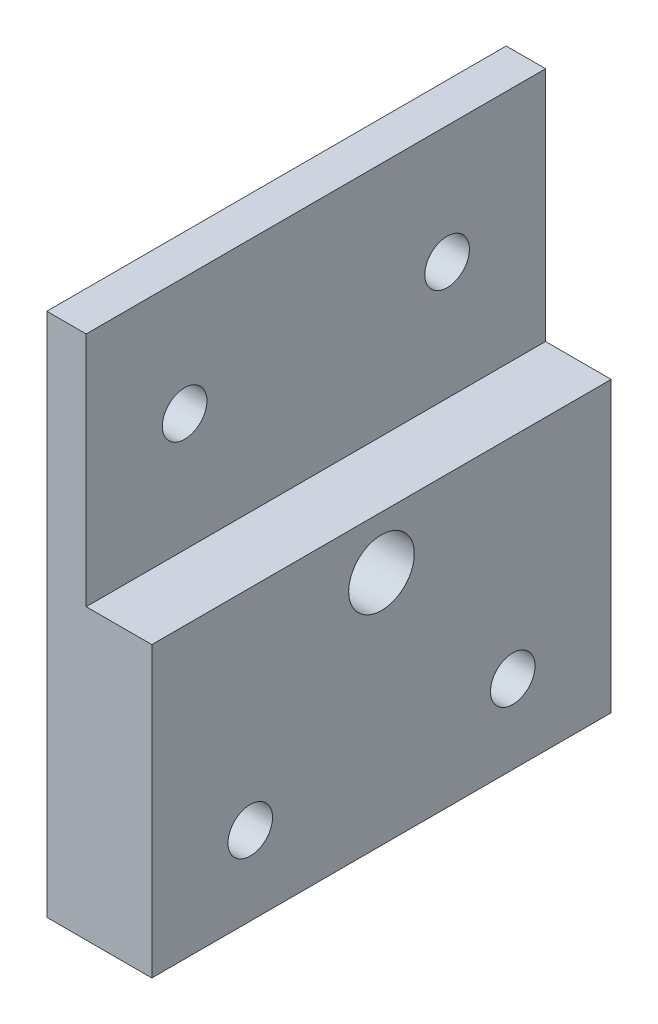
SolidWorks part; units mm, degrees
material "6061 Alloy"
ref_plane "Front Plane" through (0, 0, 0) normal (0, 0, 1) x (1, 0, 0)
ref_plane "Top Plane" through (0, 0, 0) normal (0, 1, 0) x (1, 0, 0)
ref_plane "Right Plane" through (0, 0, 0) normal (1, 0, 0) x (0, 0, -1)
sketch "Sketch1" plane through (0, 0, 0) normal (0, 0, 1) x (1, 0, 0)
  line L1 (0, 9) -> (-3, 9)
  line L2 (0, 9) -> (0, -9)
  line L3 (0, -31) -> (-3, -31)
  line L4 (-3, 9) -> (-3, -31)
  line L5 (0, -9) -> (5, -9)
  line L7 (0, -31) -> (5, -31)
  line L8 (5, -9) -> (5, -31)
  dimension "D1" = 40
  dimension "D2" = 3
  dimension "D3" = 5
  dimension "D4" = 22
  dimension "D5" = 3
extrude "Boss-Extrude1" add sketch "Sketch1" against normal blind 35
hole_wizard "M3 Clearance Hole2" positions "Sketch3" profile "Sketch2" hole size "M3" standard "ANSI Metric" end condition through all
sketch "Sketch3" plane through (-3, 0, 0) normal (-1, 0, 0) x (0, 0, 1)
  point P0 (-7.5, 0)
  point P3 (-27.5, 0)
sketch "Sketch2" plane through (-3, 0, -7.5) normal (0, 1, 0) x (0, 0, 1)
  line L0 (0, 0) -> (0, 8)
  line L1 (0, 8) -> (1.7, 8)
  line L2 (1.7, 8) -> (1.7, 0)
  line L5 (1.7, 0) -> (0, 0)
  line L11 (0, -6.35) -> (0, 107.95) construction
  dimension "Thru Hole Dia." = 3.4
  dimension "Thru Hole Depth" = 8
hole_wizard "CBORE for M3 SHCS1" positions "Sketch5" profile "Sketch4" counterbore size "M3" standard "ANSI Metric" end condition through all
sketch "Sketch5" plane through (-3, 0, 0) normal (-1, 0, 0) x (0, 0, 1)
  point P0 (-7.5, -25)
  point P3 (-27.5, -25)
sketch "Sketch4" plane through (-3, -25, -7.5) normal (0, 1, 0) x (0, 0, 1)
  line L0 (0, 0) -> (0, 8)
  line L1 (0, 8) -> (1.7, 8)
  line L3 (1.7, 8) -> (1.7, 3)
  line L4 (1.7, 3) -> (3.25, 3)
  line L5 (3.25, 3) -> (3.25, 0)
  line L7 (3.25, 0) -> (0, 0)
  line L11 (0, -6.35) -> (0, 107.95) construction
  dimension "Thru Hole Dia." = 3.4
  dimension "Thru Hole Depth" = 8
  dimension "C'Bore Dia." = 6.5
  dimension "C'Bore Depth" = 3
hole_wizard "Tap Drill for M6x1.0 Tap1" positions "Sketch7" profile "Sketch6" hole size "M6x1.0" standard "ANSI Metric" end condition through all
sketch "Sketch7" plane through (-3, 0, 0) normal (-1, 0, 0) x (0, 0, 1)
  line L4 (-17.5, -13) -> (-17.5, -31) construction
  line L5 (-35, -31) -> (0, -31) construction
  point P0 (-17.5, -13)
  dimension "D1" = 18
sketch "Sketch6" plane through (-3, -13, -17.5) normal (0, 1, 0) x (0, 0, 1)
  line L0 (0, 0) -> (0, 8)
  line L1 (0, 8) -> (2.5, 8)
  line L2 (2.5, 8) -> (2.5, 0)
  line L5 (2.5, 0) -> (0, 0)
  line L11 (0, -6.35) -> (0, 107.95) construction
  dimension "Thru Hole Dia." = 5
  dimension "Thru Hole Depth" = 8
